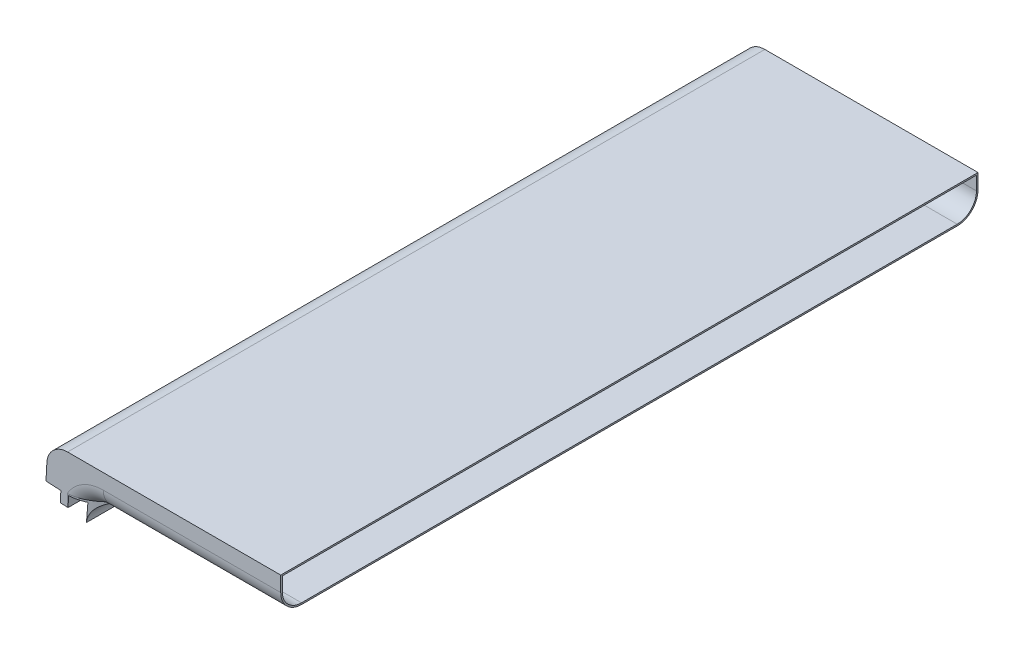
SolidWorks part; units mm, degrees
ref_plane "Front Plane" through (0, 0, 0) normal (0, 0, 1) x (1, 0, 0)
ref_plane "Top Plane" through (0, 0, 0) normal (0, 1, 0) x (1, 0, 0)
ref_plane "Right Plane" through (0, 0, 0) normal (1, 0, 0) x (0, 0, -1)
sketch "Sketch2" plane through (0, 0, 0) normal (0, 0, 1) x (1, 0, 0)
  line L0 (0, 0) -> (151.4909, 0)
  line L1 (151.4909, 0) -> (151.4909, 23.2)
  line L2 (151.4909, 23.2) -> (1.2159, 23.2)
  line L3 (1.2159, 23.2) -> (0, 0)
  dimension "D1" = 150.275
  dimension "D2" = 87
  dimension "D3" = 23.2
extrude "Boss-Extrude1" add sketch "Sketch2" along normal blind 450
fillet "Fillet1" radius 13.4 1 edges at (1.2159, 23.2, 225)
sketch "Sketch4" plane through (0, 0, 450) normal (0, 0, 1) x (1, 0, 0)
  line L0 (0, 0) -> (-1.4713, -28.0745) construction
  line L1 (0.5503, 10.5013) -> (0, 0) construction
  line L3 (24.1668, -1.2665) -> (23.5677, -12.6987)
  line L4 (0, 0) -> (36.9493, 0)
  line L5 (0, 0) -> (151.4909, 0) construction
  line L6 (0, 0) -> (24.1668, -1.2665) construction
  line L7 (0, 0) -> (9.5868, -0.5024)
  line L8 (9.5868, -0.5024) -> (9.2205, -7.4928)
  line L9 (9.2205, -7.4928) -> (14.2136, -7.7545)
  line L10 (14.2136, -7.7545) -> (14.58, -0.7641)
  line L11 (14.58, -0.7641) -> (24.1668, -1.2665)
  arc A0 (36.9493, 0) -> (23.5677, -12.6987) centre (36.9493, -13.4) ccw
  dimension "D1" = 13.4
  dimension "D2" = 5
  dimension "D3" = 7
  dimension "D4" = 3
  dimension "D5" = 24.2
extrude "Boss-Extrude2" add sketch "Sketch4" against normal through all
fillet "Fillet2" radius 13.4 4 edges at (27.7254, -3.68, 0) (27.7254, -3.68, 450) (94.2201, 0, 450) (94.2201, 0, 0)
sketch "Sketch5" plane through (0, 0, 0) normal (0, 0, 1) x (1, 0, 0)
  line L0 (0, 0) -> (-1.4713, -28.0745) construction
  line L3 (24.1668, -1.2665) -> (23.5677, -12.6987)
  line L4 (0, 0) -> (36.9493, 0)
  line L6 (0, 0) -> (24.1668, -1.2665) construction
  line L7 (0, 0) -> (9.5868, -0.5024)
  line L8 (9.5868, -0.5024) -> (9.2205, -7.4928)
  line L9 (9.2205, -7.4928) -> (14.2136, -7.7545)
  line L10 (14.2136, -7.7545) -> (14.58, -0.7641)
  line L11 (14.58, -0.7641) -> (24.1668, -1.2665)
  arc A0 (36.9493, 0) -> (23.5677, -12.6987) centre (36.9493, -13.4) ccw
  dimension "D1" = 13.4
  dimension "D2" = 5
  dimension "D3" = 7
  dimension "D4" = 3
  dimension "D5" = 24.2
extrude "Cut-Extrude1" cut sketch "Sketch5" along normal through all
shell "Shell1" thickness 1
sketch "Sketch6" plane through (0, 0, 0) normal (0, 0, 1) x (1, 0, 0)
  line L0 (0, 0) -> (-1.4713, -28.0745) construction
  line L3 (24.1668, -1.2665) -> (23.5677, -12.6987)
  line L4 (0, 0) -> (36.9493, 0)
  line L6 (0, 0) -> (24.1668, -1.2665) construction
  line L7 (0, 0) -> (9.5868, -0.5024)
  line L8 (9.5868, -0.5024) -> (9.2205, -7.4928)
  line L9 (9.2205, -7.4928) -> (14.2136, -7.7545)
  line L10 (14.2136, -7.7545) -> (14.58, -0.7641)
  line L11 (14.58, -0.7641) -> (24.1668, -1.2665)
  arc A0 (36.9493, 0) -> (23.5677, -12.6987) centre (36.9493, -13.4) ccw
  dimension "D1" = 13.4
  dimension "D2" = 5
  dimension "D3" = 7
  dimension "D4" = 3
  dimension "D5" = 24.2
extrude "Boss-Extrude3" add sketch "Sketch6" along normal up to surface (450 mm away) up to face at (51.975, 12.7829, 450)
sketch "Sketch7" plane through (0, 0, 0) normal (0, -1, 0) x (1, 0, 0)
  line L0 (13.7399, 450) -> (36.9493, 450)
  line L1 (36.9493, 450) -> (36.9493, 436.6)
  line L2 (36.9493, 13.4) -> (36.9493, 0)
  line L3 (151.4909, 0) -> (36.9493, 0) construction
  line L4 (36.9493, 13.4) -> (36.9493, 0) construction
  line L5 (36.9493, 0) -> (13.7399, 0)
  spline S0 degree 3 poles (-606.0132, -2482.6778) (-137.7745, 216.1288) (-41.0145, 460.3726) (17.7261, 449.5782) (18.2854, 449.4508) (19.3971, 449.1501) (19.9513, 448.9762) (22.6674, 448.0117) (24.6889, 446.9373) (27.0884, 445.3395) (27.5609, 445.0076) (28.4876, 444.3262) (28.9427, 443.9762) (30.2867, 442.9021) (31.1547, 442.1541) (32.8532, 440.6158) (33.6837, 439.8255) (82.5972, 392.1081) (103.7757, 303.2558) (1040.2098, 3261.0593) knots -6.334219 -6.334219 -6.334219 -6.334219 0.125 0.125 0.1875 0.1875 0.25 0.25 0.5 0.5 0.5625 0.5625 0.625 0.625 0.75 0.75 0.875 0.875 8.196167 8.196167 8.196167 8.196167 only from (13.7399, 450) to (36.9493, 436.6) construction
  spline S1 degree 3 poles (1040.2072, -2811.0512) (103.7756, 146.744) (82.5971, 57.8918) (33.6837, 10.1745) (32.8532, 9.3842) (31.1547, 7.8459) (30.2867, 7.0979) (28.9427, 6.0238) (28.4876, 5.6738) (27.5609, 4.9924) (27.0884, 4.6605) (24.6889, 3.0627) (22.6674, 1.9883) (19.9513, 1.0238) (19.3971, 0.8499) (18.2854, 0.5492) (17.7261, 0.4218) (-41.0142, -10.3725) (-137.7737, 233.8691) (-606.0073, 2932.6438) knots -7.19616 -7.19616 -7.19616 -7.19616 0.125 0.125 0.25 0.25 0.375 0.375 0.4375 0.4375 0.5 0.5 0.75 0.75 0.8125 0.8125 0.875 0.875 7.334192 7.334192 7.334192 7.334192 only from (36.9493, 13.4) to (13.7399, 0) construction
  spline S2 degree 3 poles (13.7399, 450) (14.897, 450) (16.0373, 449.8886) (17.7261, 449.5782) (18.2854, 449.4508) (19.3971, 449.1501) (19.9513, 448.9762) (22.6674, 448.0117) (24.6889, 446.9373) (27.0884, 445.3395) (27.5609, 445.0076) (28.4876, 444.3262) (28.9427, 443.9762) (30.2867, 442.9021) (31.1547, 442.1541) (32.8532, 440.6158) (33.6837, 439.8255) (35.3259, 438.2234) (36.1392, 437.4101) (36.9493, 436.6) knots 0 0 0 0 0.125 0.125 0.1875 0.1875 0.25 0.25 0.5 0.5 0.5625 0.5625 0.625 0.625 0.75 0.75 0.875 0.875 1 1 1 1
  spline S3 degree 3 poles (36.9493, 13.4) (36.1392, 12.5899) (35.3259, 11.7766) (33.6837, 10.1745) (32.8532, 9.3842) (31.1547, 7.8459) (30.2867, 7.0979) (28.9427, 6.0238) (28.4876, 5.6738) (27.5609, 4.9924) (27.0884, 4.6605) (24.6889, 3.0627) (22.6674, 1.9883) (19.9513, 1.0238) (19.3971, 0.8499) (18.2854, 0.5492) (17.7261, 0.4218) (16.0373, 0.1114) (14.897, 0) (13.7399, 0) knots 0 0 0 0 0.125 0.125 0.25 0.25 0.375 0.375 0.4375 0.4375 0.5 0.5 0.75 0.75 0.8125 0.8125 0.875 0.875 1 1 1 1
extrude "Cut-Extrude2" cut sketch "Sketch7" along normal through all
